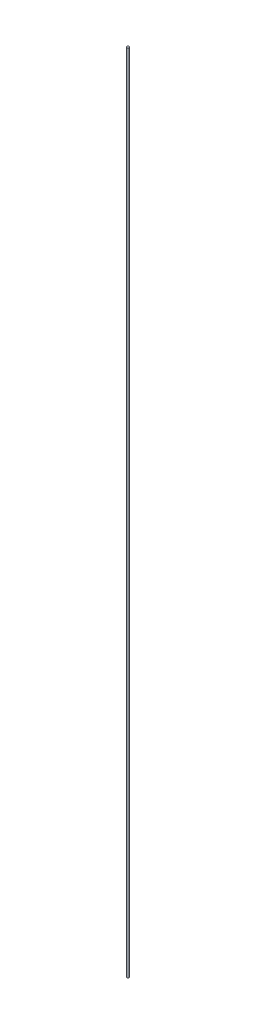
SolidWorks part; units mm, degrees
ref_plane "Front Plane" through (0, 0, 0) normal (0, 0, 1) x (1, 0, 0)
ref_plane "Top Plane" through (0, 0, 0) normal (0, 1, 0) x (1, 0, 0)
ref_plane "Right Plane" through (0, 0, 0) normal (1, 0, 0) x (0, 0, -1)
sketch "Sketch1" plane through (0, 0, 0) normal (0, 1, 0) x (1, 0, 0)
  circle A0 centre (0, 0) radius 0.75
  dimension "D1" = 1.5
extrude "Boss-Extrude1" add sketch "Sketch1" along normal blind 491
